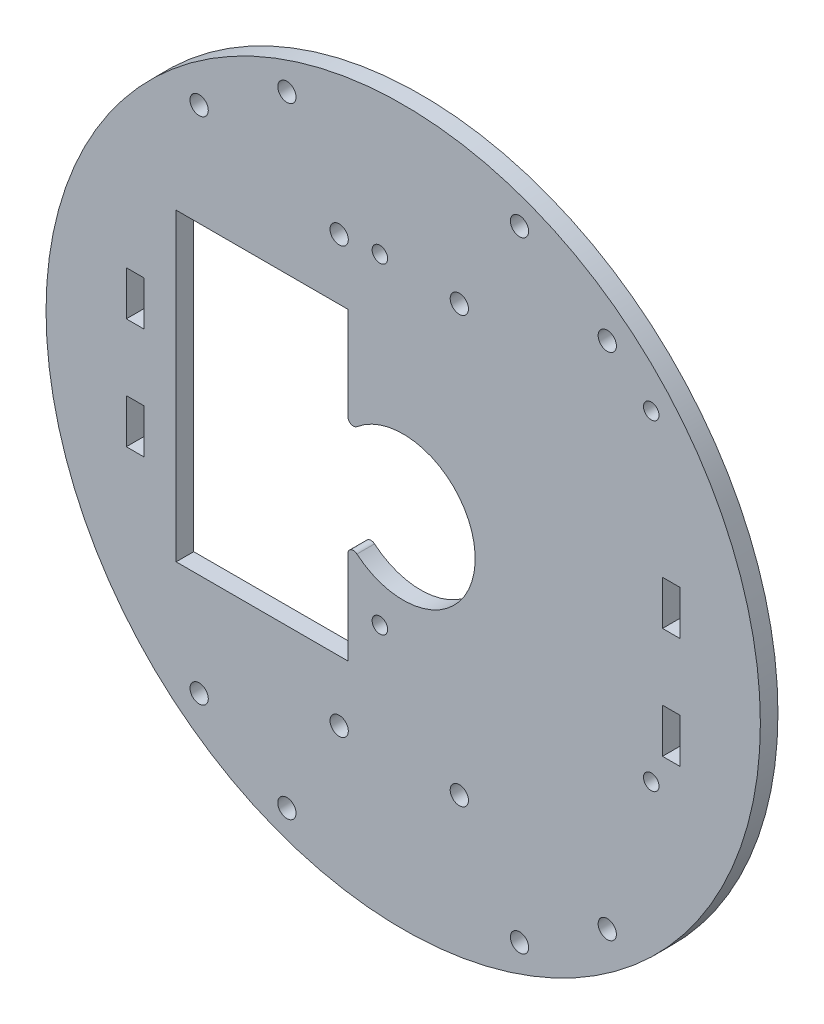
SolidWorks part; units mm, degrees
material "Acrylic (Medium-high impact)"
ref_plane "Front Plane" through (0, 0, 0) normal (0, 0, 1) x (1, 0, 0)
ref_plane "Top Plane" through (0, 0, 0) normal (0, 1, 0) x (1, 0, 0)
ref_plane "Right Plane" through (0, 0, 0) normal (1, 0, 0) x (0, 0, -1)
sketch "Sketch1" plane through (0, 0, 0) normal (0, 0, 1) x (-1, 0, 0)
  line L0 (18.6668, -38.6336) -> (-30.3332, -38.6336) construction
  line L1 (18.6668, 19.3664) -> (-30.3332, 19.3664) construction
  line L2 (14.4554, 64.8664) -> (14.4554, -64.1336) construction
  line L4 (18.6668, -42.1336) -> (-30.3332, -42.1336) construction
  line L5 (78.9554, 0.3664) -> (-50.0446, 0.3664) construction
  line L10 (18.6668, -42.1336) -> (18.6668, 42.8664) construction
  line L11 (18.6668, 42.8664) -> (-30.3332, 42.8664) construction
  line L16 (-30.3332, -42.1336) -> (-30.3332, 42.8664) construction
  circle A1 centre (14.4554, 0.3664) radius 64.5
  circle A5 centre (26.0186, -38.0586) radius 1.65
  circle A7 centre (4.3186, -38.0586) radius 1.65
  circle A8 centre (26.0186, 38.7914) radius 1.65
  circle A9 centre (4.3186, 38.7914) radius 1.65
  circle A10 centre (14.4554, 0.3664) radius 13
  circle A15 centre (-6.5446, 56.3664) radius 1.65
  circle A16 centre (-22.3949, 46.3664) radius 1.65
  circle A17 centre (35.4554, 56.3664) radius 1.65
  circle A18 centre (51.3057, 46.3664) radius 1.65
  circle A19 centre (51.3057, -45.6336) radius 1.65
  circle A20 centre (35.4554, -55.6336) radius 1.65
  circle A21 centre (-6.5446, -55.6336) radius 1.65
  circle A22 centre (-22.3949, -45.6336) radius 1.65
  circle A23 centre (18.6668, -38.6336) radius 1.4
  circle A24 centre (-30.3332, -38.6336) radius 1.4
  circle A25 centre (18.6668, 19.3664) radius 1.4
  circle A26 centre (-30.3332, 19.3664) radius 1.4
  dimension "D3" = 23.5
  dimension "D4" = 38.425
  dimension "D9" = 26
  dimension "D10" = 3.3
  dimension "D11" = 56
  dimension "D12" = 46
  dimension "D13" = 3.5
  dimension "D20" = 129
  dimension "D16" = 44.7886
  dimension "D5" = 49
  dimension "D15" = 2.8
  dimension "D6" = 21.7
  dimension "D7" = 85
  dimension "D8" = 42.5
  dimension "D14" = 21
extrude "Boss-Extrude2" add sketch "Sketch1" along normal blind 3.175
sketch "Sketch2" plane through (0, 0, 3.175) normal (0, 0, 1) x (1, 0, 0)
  line L0 (-78.9554, -0.3664) -> (50.0446, -0.3664) construction
  line L1 (35.5446, -14.3664) -> (32.3696, -14.3664)
  line L2 (35.5446, -14.3664) -> (35.5446, -6.3664)
  line L3 (35.5446, -6.3664) -> (32.3696, -6.3664)
  line L4 (32.3696, -14.3664) -> (32.3696, -6.3664)
  line L5 (35.5446, -14.3664) -> (32.3696, -6.3664) construction
  line L6 (35.5446, -6.3664) -> (32.3696, -14.3664) construction
  line L11 (50.0446, -0.3664) -> (-78.9554, -0.3664) construction
  line L12 (-14.4554, -64.8664) -> (-14.4554, 64.1336) construction
  line L13 (35.5446, 5.6336) -> (32.3696, 13.6336) construction
  line L14 (35.5446, 13.6336) -> (32.3696, 5.6336) construction
  line L15 (32.3696, 13.6336) -> (32.3696, 5.6336)
  line L16 (35.5446, 5.6336) -> (32.3696, 5.6336)
  line L17 (35.5446, 13.6336) -> (35.5446, 5.6336)
  line L18 (35.5446, 13.6336) -> (32.3696, 13.6336)
  line L19 (-64.4554, 13.6336) -> (-61.2804, 5.6336) construction
  line L20 (-64.4554, 5.6336) -> (-61.2804, 13.6336) construction
  line L21 (-64.4554, -6.3664) -> (-61.2804, -14.3664) construction
  line L22 (-64.4554, -14.3664) -> (-61.2804, -6.3664) construction
  line L23 (-64.4554, 13.6336) -> (-61.2804, 13.6336)
  line L24 (-64.4554, 13.6336) -> (-64.4554, 5.6336)
  line L25 (-64.4554, 5.6336) -> (-61.2804, 5.6336)
  line L26 (-61.2804, 13.6336) -> (-61.2804, 5.6336)
  line L27 (-61.2804, -14.3664) -> (-61.2804, -6.3664)
  line L28 (-64.4554, -6.3664) -> (-61.2804, -6.3664)
  line L29 (-64.4554, -14.3664) -> (-64.4554, -6.3664)
  line L30 (-64.4554, -14.3664) -> (-61.2804, -14.3664)
  circle A0 centre (-14.4554, -0.3664) radius 64.5 construction
  point P0 (33.9571, -10.3664)
  point P21 (33.9571, 9.6336)
  point P30 (-62.8679, 9.6336)
  point P31 (-62.8679, -10.3664)
  dimension "D1" = 8
  dimension "D2" = 3.175
  dimension "D3" = 6
  dimension "D4" = 50
extrude "Cut-Extrude1" cut sketch "Sketch2" against normal through all
sketch "Sketch3" plane through (0, 0, 3.175) normal (0, 0, 1) x (1, 0, 0)
  line L0 (-78.9554, -0.3664) -> (50.0446, -0.3664) construction
  line L1 (-55.4554, 27.1336) -> (-24.4554, 27.1336)
  line L2 (-55.4554, 27.1336) -> (-55.4554, -27.8664)
  line L3 (-55.4554, -27.8664) -> (-24.4554, -27.8664)
  line L4 (-24.4554, 27.1336) -> (-24.4554, -27.8664)
  line L5 (-55.4554, 27.1336) -> (-24.4554, -27.8664) construction
  line L6 (-55.4554, -27.8664) -> (-24.4554, 27.1336) construction
  point P0 (-39.9554, -0.3664)
  dimension "D1" = 55
  dimension "D2" = 31
  dimension "D3" = 10
extrude "Cut-Extrude2" cut sketch "Sketch3" against normal through all
fillet "Fillet3" radius 1 2 edges at (-24.4554, -8.673, 1.5875) (-24.4554, 7.9402, 1.5875)
